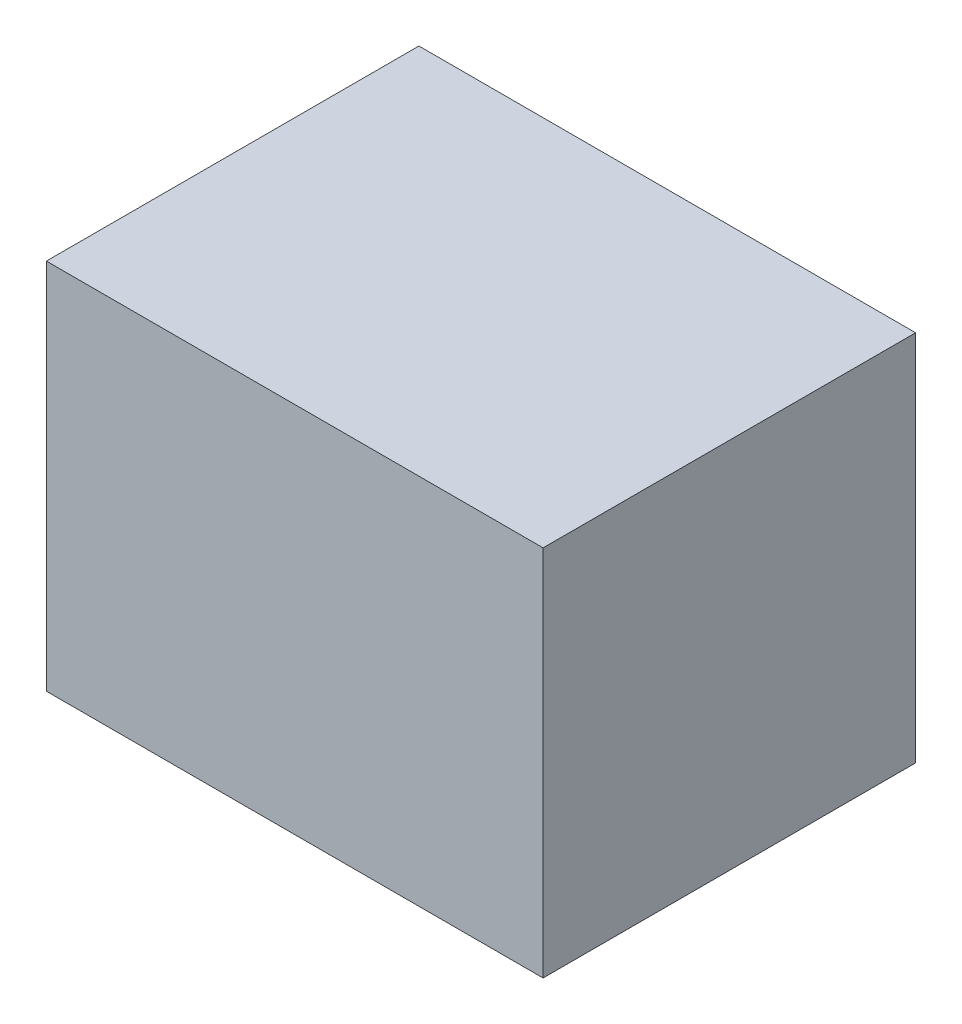
SolidWorks part; units mm, degrees
material "Balsa"
ref_plane "Front Plane" through (0, 0, 0) normal (0, 0, 1) x (1, 0, 0)
ref_plane "Top Plane" through (0, 0, 0) normal (0, 1, 0) x (1, 0, 0)
ref_plane "Right Plane" through (0, 0, 0) normal (1, 0, 0) x (0, 0, -1)
sketch "Sketch1" plane through (0, 0, 0) normal (1, 0, 0) x (0, 0, -1)
  line L0 (0, 0) -> (0, 9.525)
  line L1 (0, 9.525) -> (-9.525, 9.525)
  line L2 (-9.525, 9.525) -> (-9.525, 0)
  line L3 (-9.525, 0) -> (0, 0)
  point P3 (0, 0)
  point P6 (-19.05, 19.05)
  point P8 (0, 0)
  point P9 (0, 0)
  point P10 (0, 0)
  dimension "D1" = 9.525
extrude "Boss-Extrude1" add sketch "Sketch1" along normal mid plane 12.7
